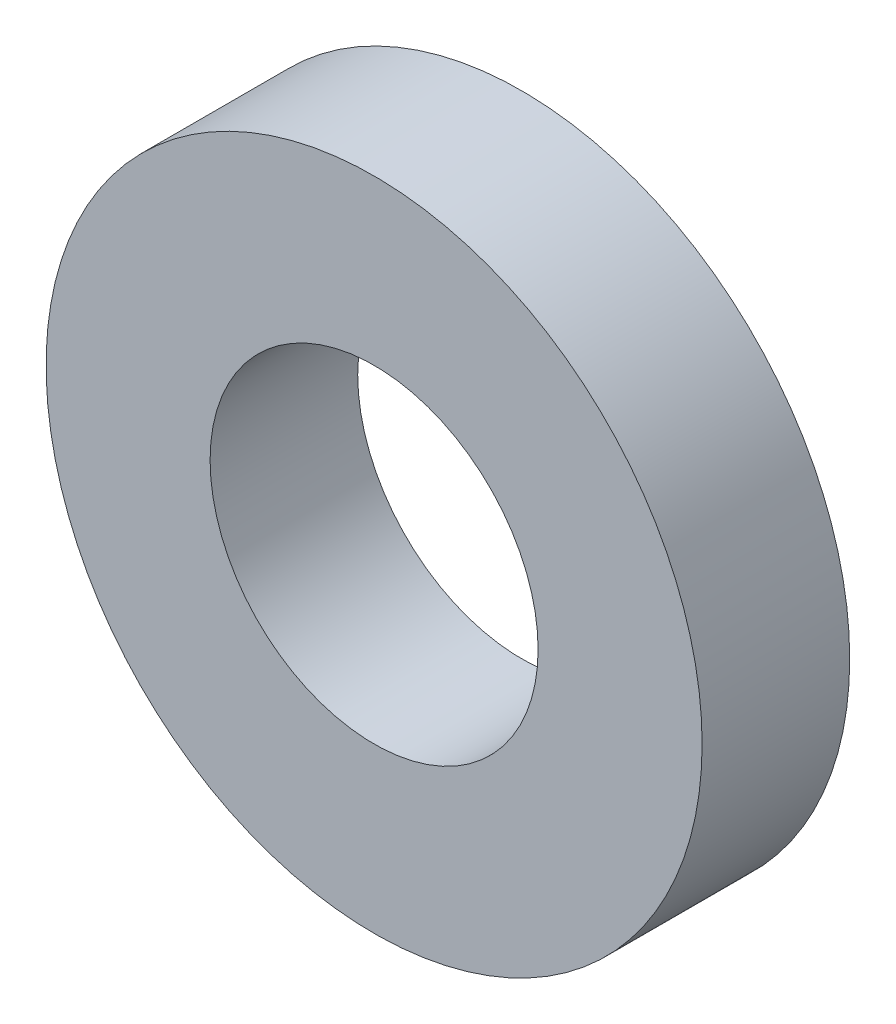
SolidWorks part; units mm, degrees
ref_plane "前视基准面" through (0, 0, 0) normal (0, 0, 1) x (1, 0, 0)
ref_plane "上视基准面" through (0, 0, 0) normal (0, 1, 0) x (1, 0, 0)
ref_plane "右视基准面" through (0, 0, 0) normal (1, 0, 0) x (0, 0, -1)
sketch "草图1" plane through (0, 0, 0) normal (0, 0, 1) x (1, 0, 0)
  circle A0 centre (0, 0) radius 40
  circle A1 centre (0, 0) radius 20
  dimension "D1" = 80
  dimension "D2" = 40
extrude "凸台-拉伸1" add sketch "草图1" along normal blind 18
